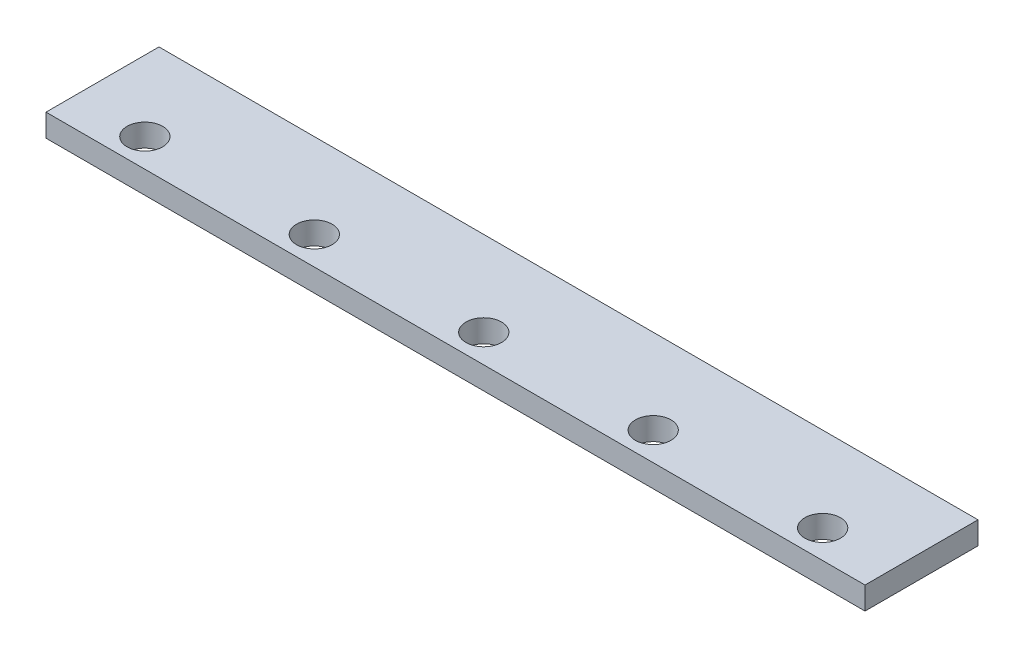
SolidWorks part; units mm, degrees
ref_plane "Front Plane" through (0, 0, 0) normal (0, 0, 1) x (1, 0, 0)
ref_plane "Top Plane" through (0, 0, 0) normal (0, 1, 0) x (1, 0, 0)
ref_plane "Right Plane" through (0, 0, 0) normal (1, 0, 0) x (0, 0, -1)
sketch "Sketch8" plane through (0, 0, 0) normal (0, 1, 0) x (1, 0, 0)
  line L0 (290, 80) -> (290, 0) construction
  line L1 (0, 0) -> (580, 0)
  line L2 (0, 0) -> (0, 80)
  line L3 (0, 80) -> (580, 80)
  line L4 (580, 0) -> (580, 80)
  circle A0 centre (530, 20) radius 12.6
  circle A1 centre (410, 20) radius 12.6
  circle A2 centre (290, 20) radius 12.6
  circle A3 centre (50, 20) radius 12.6
  circle A4 centre (170, 20) radius 12.6
  dimension "D3" = 25.2
  dimension "D6" = 120
  dimension "D8" = 120
  dimension "D1" = 580
  dimension "D2" = 80
  dimension "D4" = 50
  dimension "D5" = 20
  dimension "D7" = 20
extrude "Boss-Extrude9" add sketch "Sketch8" along normal blind 16
